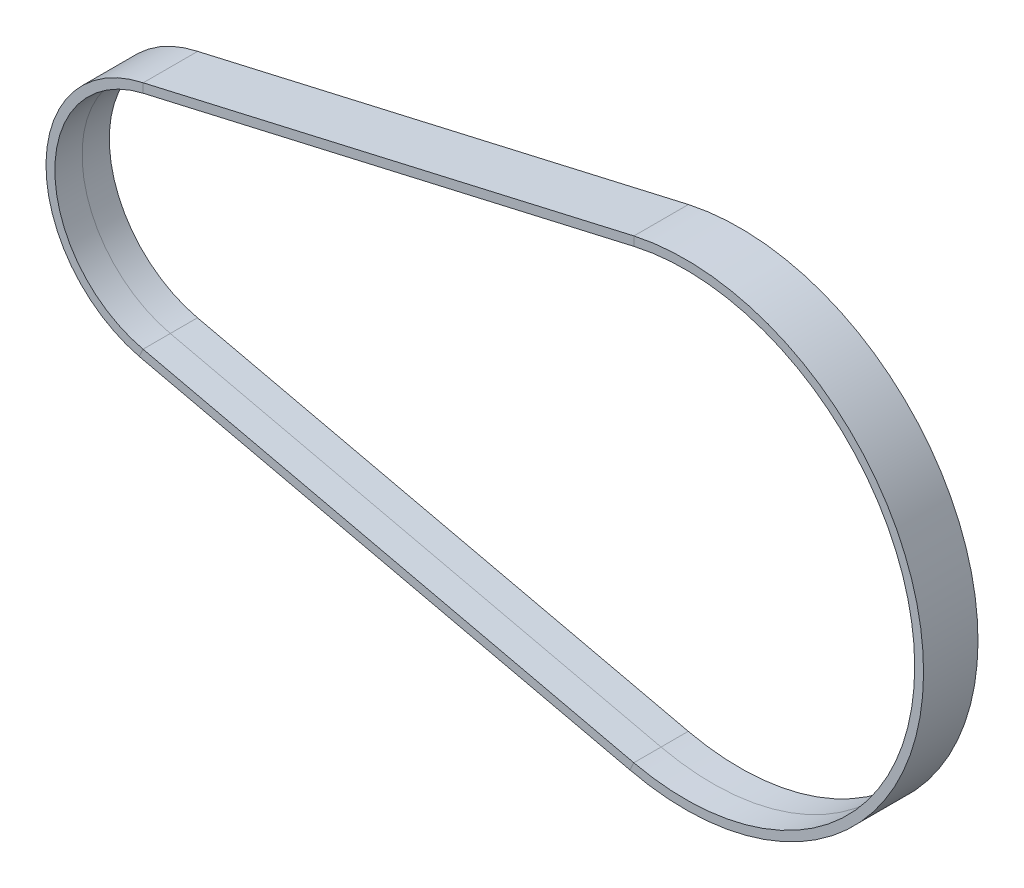
SolidWorks part; units mm, degrees
ref_plane "Front Plane" through (0, 0, 0) normal (0, 0, 1) x (1, 0, 0)
ref_plane "Top Plane" through (0, 0, 0) normal (0, 1, 0) x (1, 0, 0)
ref_plane "Right Plane" through (0, 0, 0) normal (1, 0, 0) x (0, 0, -1)
sketch "Sketch1" plane through (0, 0, 0) normal (0, 0, 1) x (1, 0, 0)
  line L0 (0, 0) -> (56.94, 0) construction
  line L1 (-2.799, 12.1826) -> (51.286, 24.6088)
  line L2 (-2.799, -12.1826) -> (51.286, -24.6088)
  arc A0 (51.286, -24.6088) -> (51.286, 24.6088) centre (56.94, 0) ccw
  arc A1 (-2.799, 12.1826) -> (-2.799, -12.1826) centre (0, 0) ccw
  dimension "D2" = 25
  dimension "D3" = 50.5
  dimension "D1" = 56.94
ref_plane "Plane1" through (-2.799, 0, 0) normal (1, 0, 0) x (0, 0, -1)
sketch "Sketch2" plane through (-2.799, 0, 0) normal (1, 0, 0) x (0, 0, -1)
  line L0 (0, 12.2197) -> (-3, 12.2197)
  line L1 (0, 25.25) -> (0, -25.25) construction
  line L2 (-3, 12.2197) -> (-3, 13.2197)
  line L3 (-3, 13.2197) -> (3, 13.2197)
  line L4 (3, 13.2197) -> (3, 12.2197)
  line L5 (3, 12.2197) -> (0, 12.2197)
  dimension "D1" = 3
  dimension "D2" = 1
  dimension "D3" = 6
sweep "Sweep1" add profiles "Sketch2" path "Sketch1"
